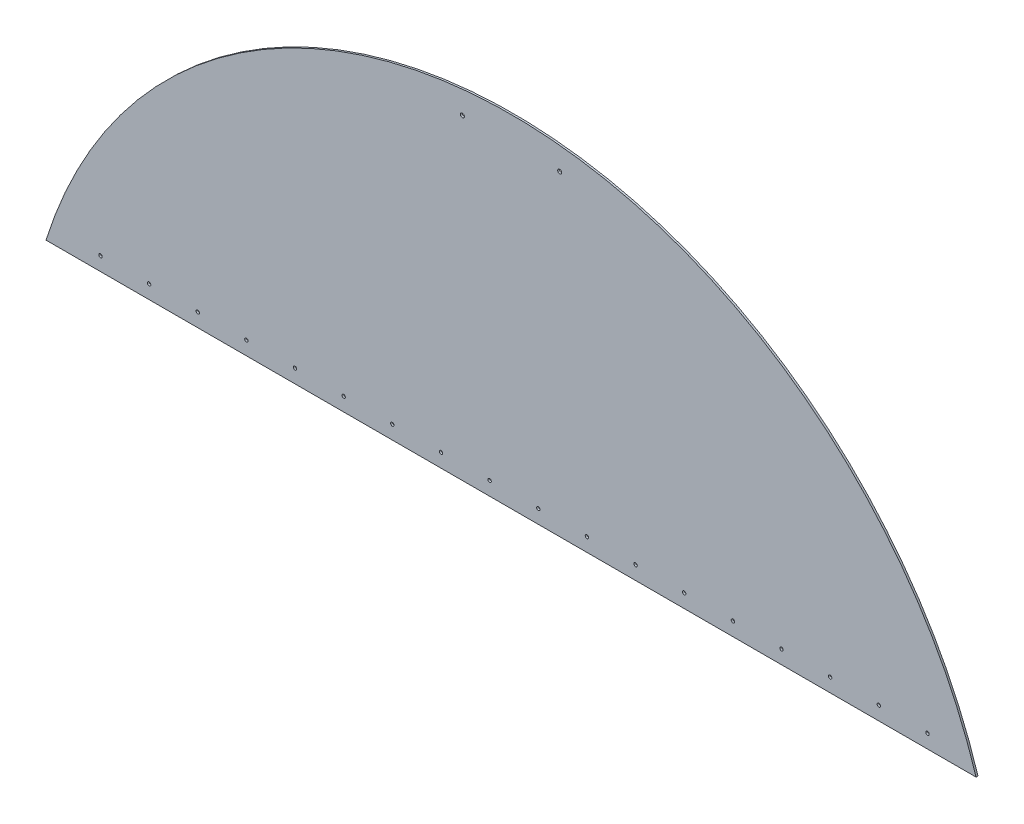
SolidWorks part; units mm, degrees
material "Wrought Stainless Steel"
ref_plane "Front Plane" through (0, 0, 0) normal (0, 0, 1) x (1, 0, 0)
ref_plane "Top Plane" through (0, 0, 0) normal (0, 1, 0) x (1, 0, 0)
ref_plane "Right Plane" through (0, 0, 0) normal (1, 0, 0) x (0, 0, -1)
sketch "Sketch1" plane through (0, 0, 0) normal (0, 0, 1) x (1, 0, 0)
  line L0 (-485.6394, 152.4) -> (485.6394, 152.4)
  arc A0 (485.6394, 152.4) -> (-485.6394, 152.4) centre (0, 0) ccw
  dimension "D1" = 508.9906
  dimension "D2" = 152.4
extrude "Boss-Extrude1" add sketch "Sketch1" along normal blind 1.9837
sketch "Sketch2" plane through (0, 0, 1.9837) normal (0, 0, 1) x (1, 0, 0)
  line L0 (-485.6394, 152.4) -> (485.6394, 152.4) construction
  circle A0 centre (434.8394, 166.6875) radius 1.778
  dimension "D1" = 3.556
  dimension "D3" = 50.8
  dimension "D2" = 14.2875
extrude "Cut-Extrude1" cut sketch "Sketch2" against normal blind 25.4
pattern_linear "LPattern1" count 18 spacing 50.8 along (-1, 0, 0) of "Cut-Extrude1"
sketch "Sketch3" plane through (0, 0, 1.9837) normal (0, 0, 1) x (1, 0, 0)
  line L0 (-485.6394, 152.4) -> (485.6394, 152.4) construction
  circle A0 centre (-50.8, 482.6) radius 2.0955
  circle A1 centre (50.8, 482.6) radius 2.0955
  dimension "D1" = 50.8
  dimension "D2" = 101.6
  dimension "D3" = 330.2
  dimension "D4" = 4.191
  dimension "D5" = 4.191
  dimension "D6" = 330.2
extrude "Cut-Extrude2" cut sketch "Sketch3" against normal blind 1.9837
